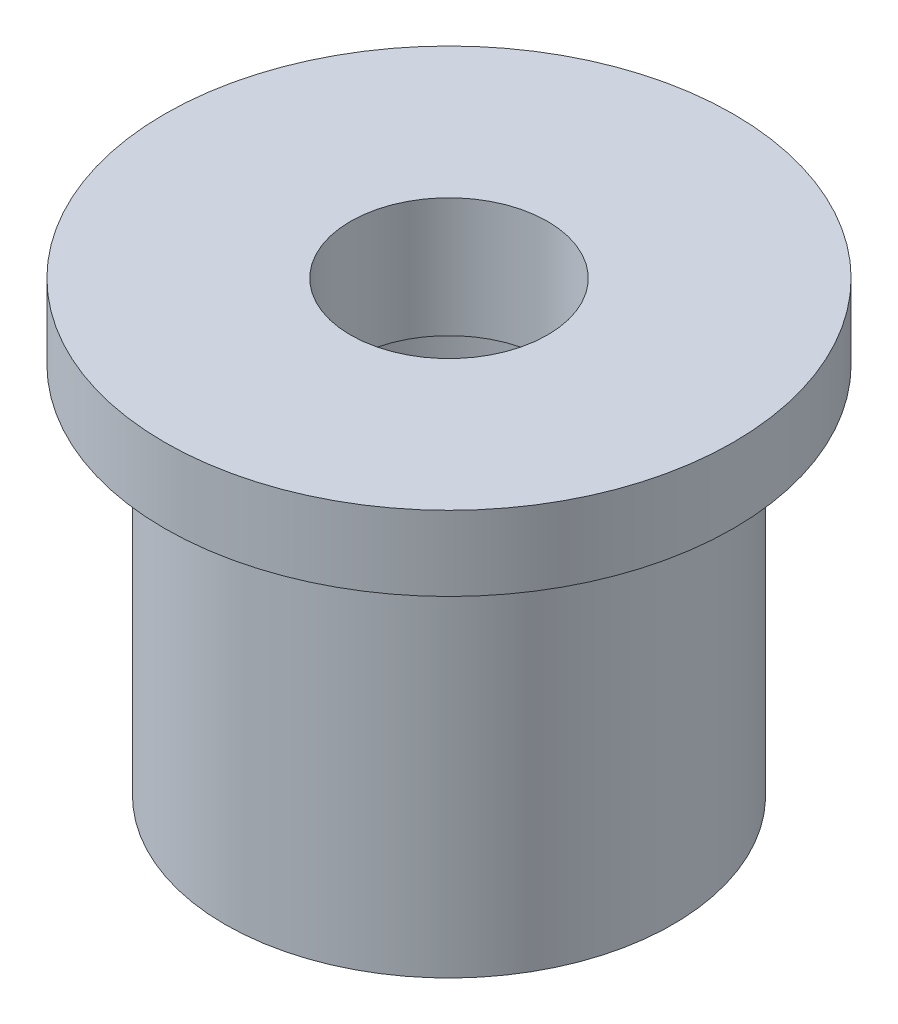
SolidWorks part; units mm, degrees
material "Polyetheretherketone (PEEK)"
ref_plane "Front Plane" through (0, 0, 0) normal (0, 0, 1) x (1, 0, 0)
ref_plane "Top Plane" through (0, 0, 0) normal (0, 1, 0) x (1, 0, 0)
ref_plane "Right Plane" through (0, 0, 0) normal (1, 0, 0) x (0, 0, -1)
sketch "Sketch1" plane through (0, 0, 0) normal (0, 0, 1) x (1, 0, 0)
  line L0 (0, 0) -> (0, 42.8538) construction
  line L1 (7.5, 0) -> (7.5, 12.5)
  line L2 (3.3, 15) -> (9.525, 15)
  line L3 (9.525, 15) -> (9.525, 12.5)
  line L4 (9.525, 12.5) -> (7.5, 12.5)
  line L5 (5, 11) -> (5, 9)
  line L6 (5, 9) -> (4.3235, 9)
  line L7 (4.3235, 9) -> (4.3235, 0) construction
  line L8 (4.3235, 0) -> (7.5, 0)
  line L9 (4.3235, 9) -> (5, 8.5)
  line L10 (5, 8.5) -> (4.3235, 8)
  line L11 (5, 9) -> (5, -0.5195) construction
  line L12 (4.3235, 8) -> (5, 7.5)
  line L13 (5, 7.5) -> (4.3235, 7)
  line L14 (4.3235, 7) -> (5, 6.5)
  line L15 (5, 6.5) -> (4.3235, 6)
  line L16 (4.3235, 6) -> (5, 5.5)
  line L17 (5, 5.5) -> (4.3235, 5)
  line L18 (4.3235, 5) -> (5, 4.5)
  line L19 (5, 4.5) -> (4.3235, 4)
  line L20 (4.3235, 4) -> (5, 3.5)
  line L21 (5, 3.5) -> (4.3235, 3)
  line L22 (4.3235, 3) -> (5, 2.5)
  line L23 (5, 2.5) -> (4.3235, 2)
  line L24 (4.3235, 2) -> (5, 1.5)
  line L25 (5, 11) -> (3.3, 11)
  line L26 (3.3, 11) -> (3.3, 15)
  line L27 (5, 1.5) -> (4.3235, 1)
  line L28 (4.3235, 1) -> (5, 0.5)
  line L29 (5, 0.5) -> (4.3235, 0)
  dimension "D1" = 15
  dimension "D2" = 19.05
  dimension "D3" = 2.5
  dimension "D4" = 15
  dimension "D5" = 2
  dimension "D6" = 10
  dimension "D7" = 4.3235
  dimension "D8" = 1
  dimension "D9" = 0.5
  dimension "D10" = 6.6
  dimension "D11" = 4
revolve "Revolve1" add sketch "Sketch1" angle 360 about L0
